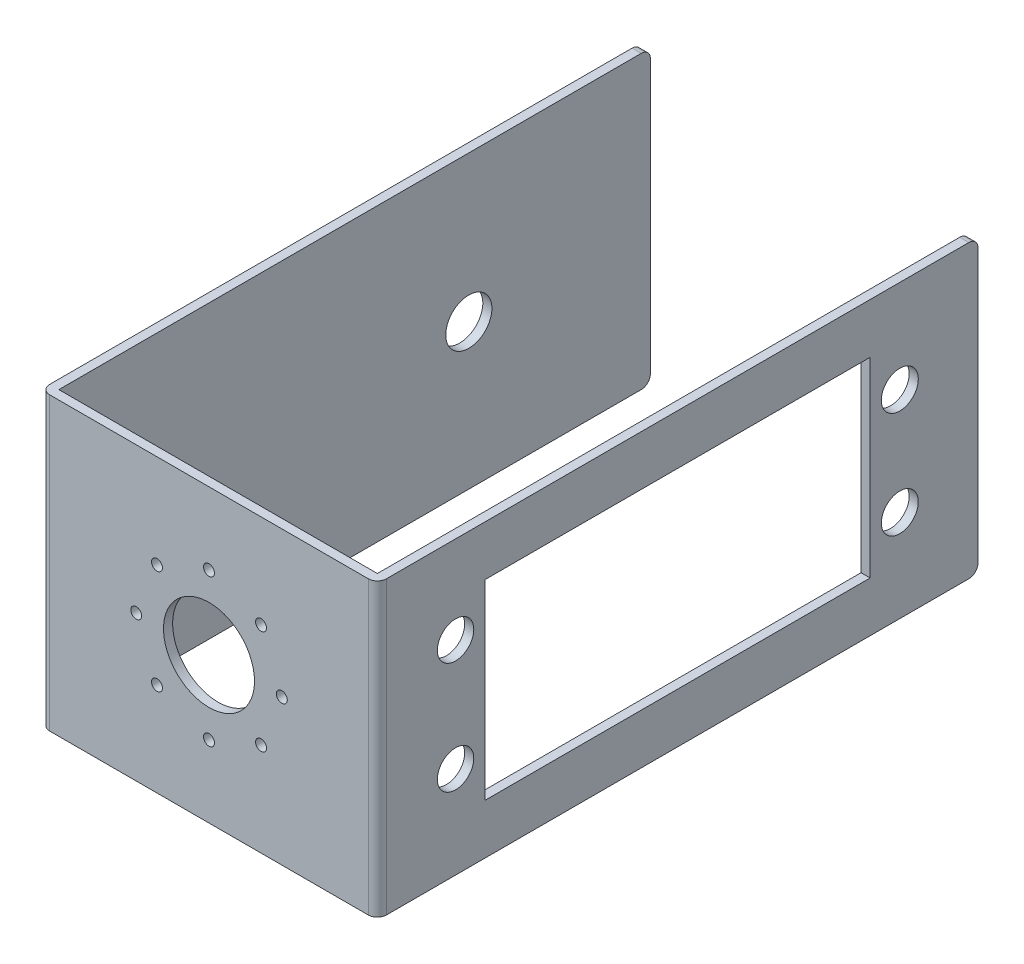
SolidWorks part; units mm, degrees
ref_plane "Front Plane" through (0, 0, 0) normal (0, 0, 1) x (1, 0, 0)
ref_plane "Top Plane" through (0, 0, 0) normal (0, 1, 0) x (1, 0, 0)
ref_plane "Right Plane" through (0, 0, 0) normal (1, 0, 0) x (0, 0, -1)
sketch "Sketch8" plane through (0, 0, 0) normal (0, 1, 0) x (1, 0, 0)
  line L0 (17.5, 0) -> (-17.5, 0)
  line L1 (-17.5, 0) -> (-17.5, 65)
  line L2 (17.5, 0) -> (17.5, 65)
  point P4 (0, 0)
extrude "Extrude-Thin2" add sketch "Sketch8" along normal blind 32 thin thin type one direction wall 1
fillet "Fillet4" radius 1 1 edges at (-18, 0, -65)
fillet "Fillet5" radius 1 1 edges at (-18, 32, -65)
fillet "Fillet6" radius 1 1 edges at (18, 0, -65)
fillet "Fillet7" radius 1 1 edges at (18, 32, -65)
fillet "Fillet8" radius 1 1 edges at (18.5, 16, 1)
fillet "Fillet9" radius 1 1 edges at (-18.5, 16, 1)
sketch "Sketch9" plane through (18.5, 0, 0) normal (1, 0, 0) x (0, 0, -1)
  line L0 (53.1474, 26.5) -> (10.8526, 26.5)
  line L8 (10.8526, 26.5) -> (10.8526, 5.5)
  line L9 (10.8526, 5.5) -> (53.1474, 5.5)
  line L10 (53.1474, 5.5) -> (53.1474, 26.5)
  point P4 (32, 26.5)
extrude "Cut-Extrude2" cut sketch "Sketch9" against normal blind 32
sketch "Sketch10" plane through (0, 0, 1) normal (0, 0, 1) x (1, 0, 0)
  circle A0 centre (0, 16) radius 5
extrude "Cut-Extrude3" cut sketch "Sketch10" against normal blind 32
sketch "Sketch11" plane through (18.5, 0, 0) normal (1, 0, 0) x (0, 0, -1)
  circle A0 centre (56.4061, 21.7936) radius 2.0326
  circle A1 centre (56.4061, 10.1156) radius 2.0281
sketch "Sketch13" plane through (-18.5, 0, 0) normal (-1, 0, 0) x (0, 0, 1)
  circle A0 centre (-45.0496, 15.9398) radius 2.536
sketch "Sketch14" plane through (0, 0, 1) normal (0, 0, 1) x (1, 0, 0)
  circle A1 centre (0, 7.9149) radius 0.6
  circle A2 centre (0, 24.0851) radius 0.6
  circle A3 centre (-5.717, 10.283) radius 0.6
  circle A4 centre (-5.717, 21.717) radius 0.6
  circle A5 centre (5.717, 10.283) radius 0.6
  circle A6 centre (5.717, 21.717) radius 0.6
extrude "Cut-Extrude7" cut sketch "Sketch14" against normal blind 32
sketch "Sketch15" plane through (0, 0, 1) normal (0, 0, 1) x (1, 0, 0)
  circle A1 centre (-8, 16) radius 0.6
  circle A2 centre (8, 16) radius 0.6
extrude "Cut-Extrude8" cut sketch "Sketch15" against normal blind 10
extrude "Cut-Extrude9" cut sketch "Sketch13" against normal blind 10 contours A0
extrude "Cut-Extrude12" cut sketch "Sketch11" against normal blind 10
sketch "Sketch16" plane through (18.5, 0, 0) normal (1, 0, 0) x (0, 0, -1)
  circle A0 centre (7.5926, 22.3853) radius 2
  circle A1 centre (7.5926, 10.1156) radius 2
extrude "Cut-Extrude13" cut sketch "Sketch16" against normal blind 10
